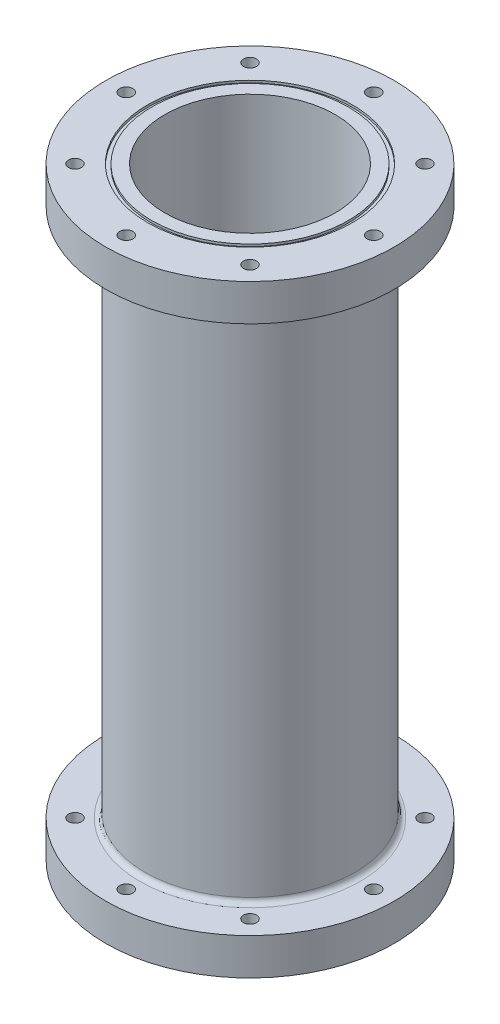
SolidWorks part; units mm, degrees
ref_plane "Front Plane" through (0, 0, 0) normal (0, 0, 1) x (1, 0, 0)
ref_plane "Top Plane" through (0, 0, 0) normal (0, 1, 0) x (1, 0, 0)
ref_plane "Right Plane" through (0, 0, 0) normal (1, 0, 0) x (0, 0, -1)
sketch "Sketch2" plane through (0, 0, 0) normal (0, 1, 0) x (1, 0, 0)
  circle A0 centre (0, 0) radius 41.275
  circle A1 centre (0, 0) radius 50.8
  dimension "D1" = 101.6
  dimension "D2" = 82.55
extrude "Base Cylinder" add sketch "Sketch2" along normal blind 292.1
sketch "Sketch3" plane through (0, 0, 0) normal (0, -1, 0) x (1, 0, 0)
  circle A0 centre (0, 0) radius 41.275
  circle A1 centre (0, 0) radius 69.85
  dimension "D1" = 139.7
extrude "Aft Flange" add sketch "Sketch3" against normal blind 17.78
sketch "Sketch4" plane through (0, 292.1, 0) normal (0, 1, 0) x (1, 0, 0)
  circle A0 centre (0, 0) radius 41.275
  circle A1 centre (0, 0) radius 69.85
extrude "Forward Flange" add sketch "Sketch4" against normal blind 17.78
sketch "Sketch6" plane through (0, 0, 0) normal (0, -1, 0) x (1, 0, 0)
  circle A0 centre (0, 0) radius 49.53
  circle A1 centre (0, 0) radius 47.625
  dimension "D1" = 99.06
  dimension "D2" = 95.25
extrude "O-Ring Slot 1" cut sketch "Sketch6" against normal blind 1.1176
sketch "Sketch7" plane through (0, 292.1, 0) normal (0, 1, 0) x (1, 0, 0)
  circle A0 centre (0, 0) radius 49.53
  circle A1 centre (0, 0) radius 47.625
  dimension "D1" = 99.06
  dimension "D2" = 95.25
extrude "O-Ring Slot 2" cut sketch "Sketch7" against normal blind 1.1176
sketch "Sketch8" plane through (0, 0, 0) normal (0, -1, 0) x (1, 0, 0)
  circle A0 centre (-59.9186, 0) radius 3.175
  circle A1 centre (-42.3688, 42.3688) radius 3.175
  circle A2 centre (0, 59.9186) radius 3.175
  circle A3 centre (42.3688, 42.3688) radius 3.175
  circle A4 centre (59.9186, 0) radius 3.175
  circle A5 centre (42.3688, -42.3688) radius 3.175
  circle A6 centre (0, -59.9186) radius 3.175
  circle A7 centre (-42.3688, -42.3688) radius 3.175
  point P36 (0, 0)
  dimension "D2" = 6.35
  dimension "D1" = 59.9186
  dimension "D3" = 8
extrude "Cut-Extrude4" cut sketch "Sketch8" against normal through all both and the other way through all
fillet "Fillet1" radius 2.54 2 edges at (0, 17.78, -50.8) (0, 274.32, 50.8)
